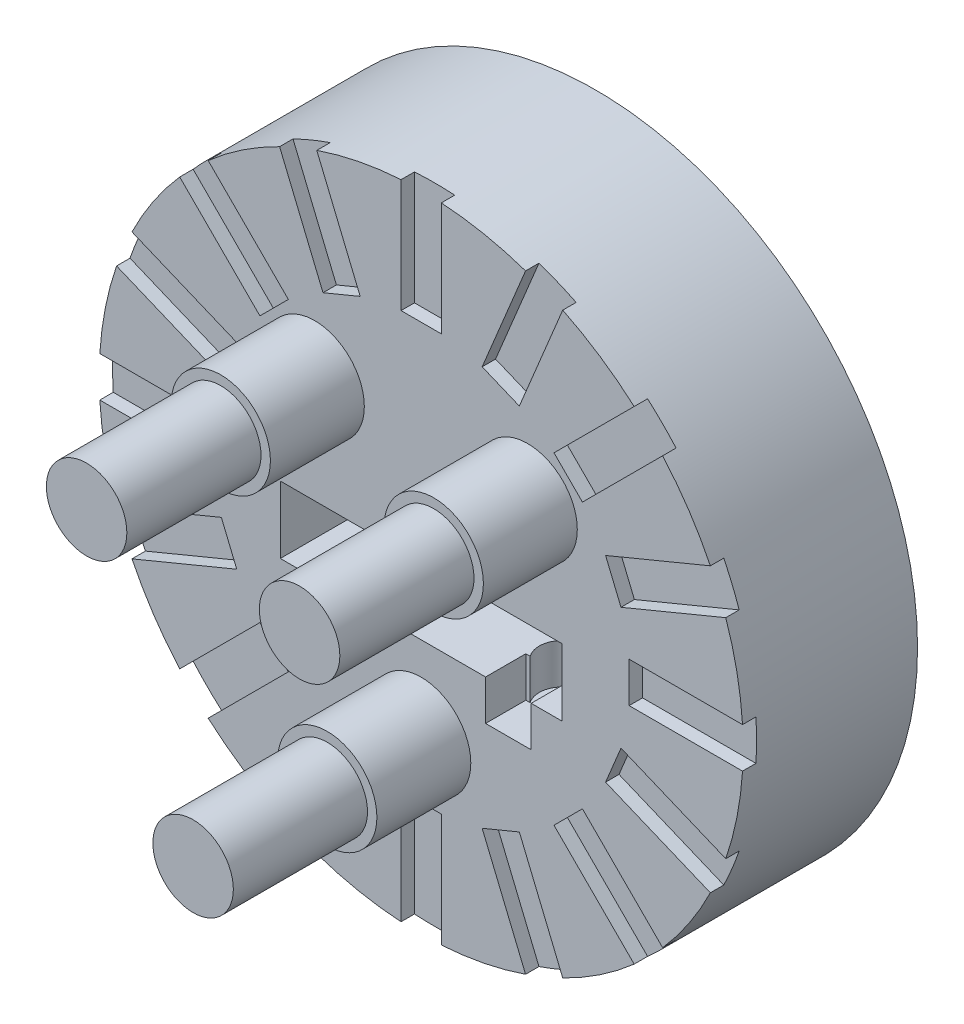
SolidWorks part; units mm, degrees
ref_plane "Front" through (0, 0, 0) normal (0, 0, 1) x (1, 0, 0)
ref_plane "Top" through (0, 0, 0) normal (0, 1, 0) x (1, 0, 0)
ref_plane "Right" through (0, 0, 0) normal (1, 0, 0) x (0, 0, -1)
sketch "Sketch1" plane through (0, 0, 0) normal (0, 0, 1) x (1, 0, 0)
  circle A0 centre (0, 0) radius 24
extrude "Extrude1" add sketch "Sketch1" along normal blind 5
sketch "Sketch2" plane through (0, 0, 5) normal (0, 0, 1) x (1, 0, 0)
  line L0 (-2.5, 0) -> (-10.5, 0)
  line L1 (2.5, 0) -> (10.5, 0)
  line L2 (10.5, 0) -> (10.5, -5)
  line L3 (10.5, -5) -> (-10.5, -5)
  line L4 (-10.5, -5) -> (-10.5, 0)
  circle A0 centre (0, 0) radius 2.5 construction
  arc A1 (2.5, 0) -> (-2.5, 0) centre (0, 0) cw
  circle A2 centre (0, 0) radius 24
extrude "Extrude2" add sketch "Sketch2" along normal blind 8
sketch "Sketch3" plane through (0, 0, 13) normal (0, 0, 1) x (1, 0, 0)
  circle A0 centre (0, 0) radius 2.5
  circle A1 centre (-7.9375, 7.9375) radius 3.7
  circle A2 centre (7.9375, 7.9375) radius 3.7
  circle A3 centre (0, -11.1125) radius 3.7
extrude "Extrude3" add sketch "Sketch3" along normal blind 7
sketch "Sketch5" plane through (0, 0, 20) normal (0, 0, 1) x (1, 0, 0)
  circle A0 centre (-7.9375, 7.9375) radius 3
  circle A1 centre (7.9375, 7.9375) radius 3
  circle A2 centre (0, -11.1125) radius 3
extrude "Extrude6" add sketch "Sketch5" along normal blind 10
sketch "Sketch6" plane through (0, 0, 0) normal (0, 0, -1) x (-1, 0, 0)
  circle A0 centre (0, 12.7) radius 3.175
  circle A1 centre (7.9375, -11.1125) radius 3.175
  circle A2 centre (-7.9375, -11.1125) radius 3.175
extrude "Extrude7" cut sketch "Sketch6" against normal blind 3
sketch "Sketch7" plane through (0, 0, 0) normal (0, -1, 0) x (1, 0, 0)
  line L0 (10.5, 5) -> (2.5, 13) construction
  line L1 (24, 13) -> (-24, 13) construction
  line L2 (2.5, 13) -> (2.5, 5) construction
  line L3 (10.5, 13) -> (2.5, 5) construction
  line L4 (-10.5, 13) -> (-2.5, 5) construction
  line L5 (-2.5, 13) -> (-2.5, 5) construction
  line L6 (-10.5, 5) -> (10.5, 5) construction
  line L7 (-2.5, 13) -> (-10.5, 5) construction
  circle A0 centre (-6.5, 9) radius 1.7
  circle A1 centre (6.5, 9) radius 1.7
  point P11 (6.5, 9)
  point P23 (-6.5, 9)
  dimension "D1" = 21
  dimension "D2" = 8
extrude "Extrude8" cut sketch "Sketch7" against normal blind 3 and the other way blind 8
sketch "Sketch8" plane through (0, 0, 13) normal (0, 0, 1) x (1, 0, 0)
  line L0 (-8.2, -5) -> (-8.2, -8)
  line L1 (-8.2, -8) -> (-4.8, -8)
  line L2 (-4.8, -8) -> (-4.8, -5)
  line L3 (-4.8, -5) -> (-8.2, -5)
  line L4 (4.8, -5) -> (4.8, -8)
  line L5 (4.8, -8) -> (8.2, -8)
  line L6 (8.2, -8) -> (8.2, -5)
  line L7 (8.2, -5) -> (4.8, -5)
  point P0 (-4.8, -5)
  point P1 (-4.8, -8)
  point P3 (-8.2, -8)
  point P5 (-8.2, -5)
  point P7 (4.8, -5)
  point P9 (4.8, -8)
  point P11 (8.2, -8)
  point P13 (8.2, -5)
extrude "Extrude9" cut sketch "Sketch8" against normal blind 3
sketch "Sketch9" plane through (0, 0, 13) normal (0, 0, 1) x (1, 0, 0)
  line L0 (0, 0) -> (25.4, 25.4) construction
  line L1 (0, 0) -> (-25.4, 25.4) construction
  line L2 (0, 0) -> (25.4, -25.4) construction
  line L3 (0, 0) -> (-25.4, -25.4) construction
  line L4 (0, 0) -> (22.1731, 9.1844) construction
  line L5 (0, 0) -> (-9.1844, 22.1731) construction
  line L6 (0, 0) -> (22.1731, -9.1844) construction
  line L7 (0, 0) -> (-9.1844, -22.1731) construction
  line L8 (-9.1844, 22.1731) -> (9.1844, -22.1731) construction
  line L9 (22.1731, -9.1844) -> (-22.1731, 9.1844) construction
  line L10 (22.1731, 9.1844) -> (-22.1731, -9.1844) construction
  line L11 (-9.1844, -22.1731) -> (9.1844, 22.1731) construction
  line L12 (24, 0) -> (-24, 0) construction
  line L13 (0, 24) -> (0, -24) construction
  line L14 (24, 0) -> (24, -1.5)
  line L15 (24, 0) -> (24, 1.5)
  line L16 (24, 1.5) -> (15.5, 1.5)
  line L17 (15.5, 1.5) -> (15.5, -1.5)
  line L18 (15.5, -1.5) -> (24, -1.5)
  line L19 (22.1731, 9.1844) -> (22.7471, 7.7986)
  line L20 (22.1731, 9.1844) -> (21.5991, 10.5702)
  line L21 (21.5991, 10.5702) -> (13.7461, 7.3174)
  line L22 (13.7461, 7.3174) -> (14.8942, 4.5458)
  line L23 (22.7471, 7.7986) -> (14.8942, 4.5458)
  line L24 (16.9706, 16.9706) -> (18.0312, 15.9099)
  line L25 (16.9706, 16.9706) -> (15.9099, 18.0312)
  line L26 (15.9099, 18.0312) -> (9.8995, 12.0208)
  line L27 (18.0312, 15.9099) -> (12.0208, 9.8995)
  line L28 (12.0208, 9.8995) -> (9.8995, 12.0208)
  line L29 (9.1844, 22.1731) -> (10.5702, 21.5991)
  line L30 (9.1844, 22.1731) -> (7.7986, 22.7471)
  line L31 (10.5702, 21.5991) -> (7.3174, 13.7461)
  line L32 (7.7986, 22.7471) -> (4.5458, 14.8942)
  line L33 (4.5458, 14.8942) -> (7.3174, 13.7461)
  line L34 (0, 24) -> (1.5, 24)
  line L35 (0, 24) -> (-1.5, 24)
  line L36 (1.5, 24) -> (1.5, 15.5)
  line L37 (-1.5, 24) -> (-1.5, 15.5)
  line L38 (-1.5, 15.5) -> (1.5, 15.5)
  line L39 (-9.1844, 22.1731) -> (-7.7986, 22.7471)
  line L40 (-9.1844, 22.1731) -> (-10.5702, 21.5991)
  line L41 (-10.5702, 21.5991) -> (-7.3174, 13.7461)
  line L42 (-7.3174, 13.7461) -> (-4.5458, 14.8942)
  line L43 (-4.5458, 14.8942) -> (-7.7986, 22.7471)
  line L44 (-16.9706, 16.9706) -> (-15.9099, 18.0312)
  line L45 (-15.9099, 18.0312) -> (-9.8995, 12.0208)
  line L46 (-9.8995, 12.0208) -> (-12.0208, 9.8995)
  line L47 (-16.9706, 16.9706) -> (-18.0312, 15.9099)
  line L48 (-18.0312, 15.9099) -> (-12.0208, 9.8995)
  line L49 (-22.1731, 9.1844) -> (-21.5991, 10.5702)
  line L50 (-21.5991, 10.5702) -> (-13.7461, 7.3174)
  line L51 (-22.1731, 9.1844) -> (-22.7471, 7.7986)
  line L52 (-22.7471, 7.7986) -> (-14.8942, 4.5458)
  line L53 (-14.8942, 4.5458) -> (-13.7461, 7.3174)
  line L54 (-24, 0) -> (-24, 1.5)
  line L55 (-24, 1.5) -> (-15.5, 1.5)
  line L56 (-24, 0) -> (-24, -1.5)
  line L57 (-24, -1.5) -> (-15.5, -1.5)
  line L58 (-15.5, -1.5) -> (-15.5, 1.5)
  line L59 (-22.1731, -9.1844) -> (-22.7471, -7.7986)
  line L60 (-22.7471, -7.7986) -> (-14.8942, -4.5458)
  line L61 (-14.8942, -4.5458) -> (-13.7461, -7.3174)
  line L62 (-22.1731, -9.1844) -> (-21.5991, -10.5702)
  line L63 (-21.5991, -10.5702) -> (-13.7461, -7.3174)
  line L64 (-16.9706, -16.9706) -> (-15.9099, -18.0312)
  line L65 (-16.9706, -16.9706) -> (-18.0312, -15.9099)
  line L66 (-15.9099, -18.0312) -> (-9.8995, -12.0208)
  line L67 (-18.0312, -15.9099) -> (-12.0208, -9.8995)
  line L68 (-12.0208, -9.8995) -> (-9.8995, -12.0208)
  line L69 (-9.1844, -22.1731) -> (-7.7986, -22.7471)
  line L70 (-9.1844, -22.1731) -> (-10.5702, -21.5991)
  line L71 (-10.5702, -21.5991) -> (-7.3174, -13.7461)
  line L72 (-7.3174, -13.7461) -> (-4.5458, -14.8942)
  line L73 (-4.5458, -14.8942) -> (-7.7986, -22.7471)
  line L74 (0, -24) -> (1.5, -24)
  line L75 (1.5, -24) -> (1.5, -15.5)
  line L76 (1.5, -15.5) -> (-1.5, -15.5)
  line L77 (0, -24) -> (-1.5, -24)
  line L78 (-1.5, -24) -> (-1.5, -15.5)
  line L79 (9.1844, -22.1731) -> (10.5702, -21.5991)
  line L80 (10.5702, -21.5991) -> (7.3174, -13.7461)
  line L81 (7.3174, -13.7461) -> (4.5458, -14.8942)
  line L82 (4.5458, -14.8942) -> (7.7986, -22.7471)
  line L83 (7.7986, -22.7471) -> (9.1844, -22.1731)
  line L84 (16.9706, -16.9706) -> (18.0312, -15.9099)
  line L85 (18.0312, -15.9099) -> (12.0208, -9.8995)
  line L86 (12.0208, -9.8995) -> (9.8995, -12.0208)
  line L87 (16.9706, -16.9706) -> (15.9099, -18.0312)
  line L88 (15.9099, -18.0312) -> (9.8995, -12.0208)
  line L89 (22.1731, -9.1844) -> (22.7471, -7.7986)
  line L90 (22.7471, -7.7986) -> (14.8942, -4.5458)
  line L91 (14.8942, -4.5458) -> (13.7461, -7.3174)
  line L92 (22.1731, -9.1844) -> (21.5991, -10.5702)
  line L93 (21.5991, -10.5702) -> (13.7461, -7.3174)
  circle A0 centre (0, 0) radius 24 construction
  circle A1 centre (0, 0) radius 24 construction
  point P0 (-24, 0)
  point P1 (24, 0)
  point P4 (0, 24)
  point P5 (0, -24)
  point P13 (16.9706, 16.9706)
  point P14 (16.9706, -16.9706)
  point P15 (-16.9706, -16.9706)
  point P52 (-16.9706, 16.9706)
extrude "Extrude10" cut sketch "Sketch9" against normal blind 1
